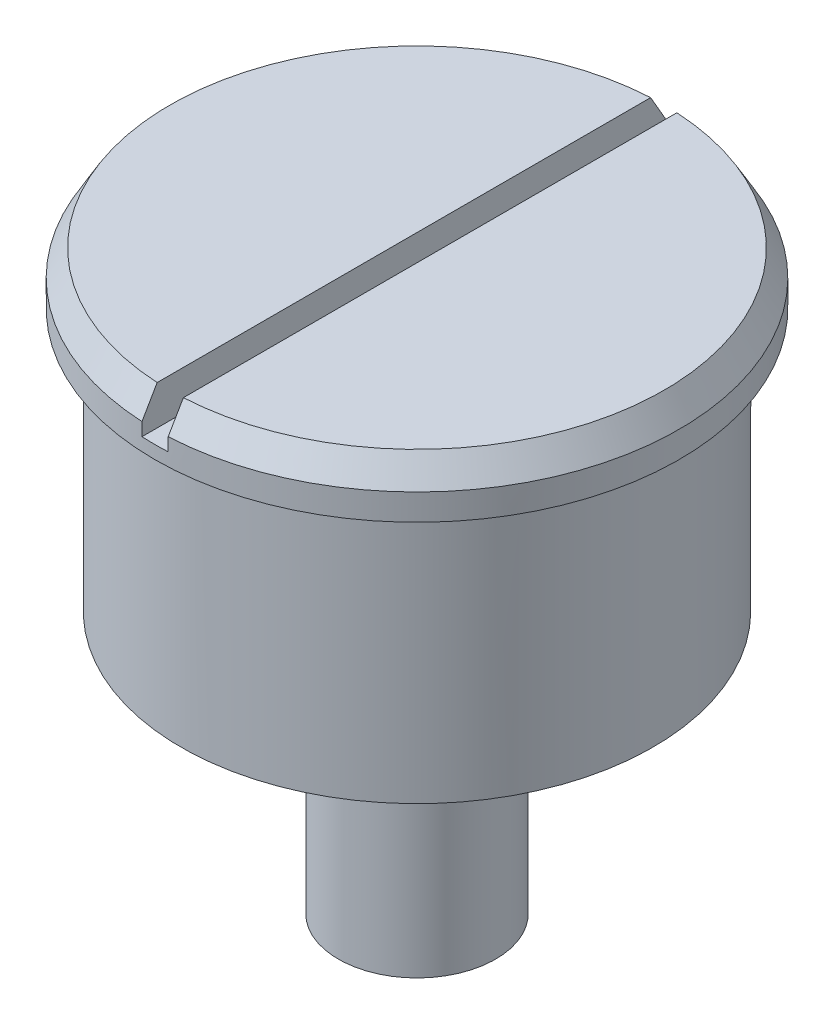
SolidWorks part; units mm, degrees
ref_plane "Alzado" through (0, 0, 0) normal (0, 0, 1) x (1, 0, 0)
ref_plane "Planta" through (0, 0, 0) normal (0, 1, 0) x (1, 0, 0)
ref_plane "Vista lateral" through (0, 0, 0) normal (1, 0, 0) x (0, 0, -1)
sketch "Croquis1" plane through (0, 0, 0) normal (0, 1, 0) x (1, 0, 0)
  circle A0 centre (0, 0) radius 4.5
extrude "Saliente-Extruir1" add sketch "Croquis1" along normal blind 4
sketch "Croquis2" plane through (0, 4, 0) normal (0, 1, 0) x (1, 0, 0)
  circle A0 centre (0, 0) radius 5
extrude "Saliente-Extruir2" add sketch "Croquis2" along normal blind 1
sketch "Croquis3" plane through (0, 0, 0) normal (0, 0, 1) x (1, 0, 0)
  line L0 (0.25, 8.4179) -> (-0.25, 8.4179)
  line L2 (0.25, 8.4179) -> (0.25, 4.25)
  line L4 (0.25, 4.25) -> (-0.25, 4.25)
  line L5 (-0.25, 4.25) -> (-0.25, 8.4179)
  line L6 (-5, 4) -> (5, 4) construction
  point P5 (0, 8.4179)
  dimension "D1" = 0.25
extrude "Cortar-Extruir1" cut sketch "Croquis3" against normal through all both and the other way through all
chamfer "Chaflán1" distance 0.5 angle 30 2 edges at (5, 5, 0) (-5, 5, 0)
sketch "Croquis4" plane through (0, 0, 0) normal (0, -1, 0) x (1, 0, 0)
  circle A0 centre (0, 0) radius 4.5
extrude "Saliente-Extruir3" add sketch "Croquis4" along normal blind 1
sketch "Croquis5" plane through (0, -1, 0) normal (0, -1, 0) x (-1, 0, 0)
  circle A0 centre (0, 0) radius 1.5
extrude "Saliente-Extruir4" add sketch "Croquis5" along normal blind 5
cosmetic thread "Rosca cosmética1" parameters "D2"=2.439
